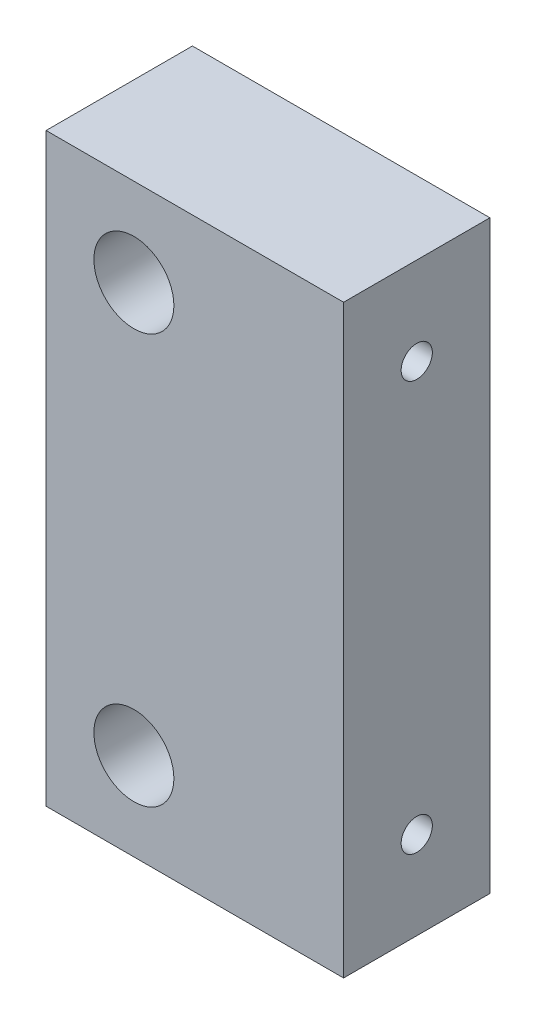
SolidWorks part; units mm, degrees
ref_plane "Front Plane" through (0, 0, 0) normal (0, 0, 1) x (1, 0, 0)
ref_plane "Top Plane" through (0, 0, 0) normal (0, 1, 0) x (1, 0, 0)
ref_plane "Right Plane" through (0, 0, 0) normal (1, 0, 0) x (0, 0, -1)
sketch "Sketch1" plane through (0, 0, 0) normal (0, 1, 0) x (1, 0, 0)
  line L1 (-15.25, 7.5) -> (15.25, 7.5)
  line L2 (-15.25, 7.5) -> (-15.25, -7.5)
  line L3 (-15.25, -7.5) -> (15.25, -7.5)
  line L4 (15.25, 7.5) -> (15.25, -7.5)
  point P4 (0, 7.5)
  point P6 (15.25, 0)
  dimension "D1" = 15
  dimension "D2" = 30.5
extrude "Boss-Extrude1" add sketch "Sketch1" along normal blind 60
sketch "Sketch2" plane through (0, 0, 7.5) normal (0, 0, 1) x (1, 0, 0)
  line L2 (-15.25, 0) -> (15.25, 0) construction
  line L4 (-15.25, 60) -> (-15.25, 0) construction
  circle A0 centre (-6.25, 51) radius 4.1
  circle A1 centre (-6.25, 9) radius 4.1
  dimension "D1" = 9
  dimension "D2" = 42
  dimension "D3" = 9
  dimension "D4" = 9
extrude "Cut-Extrude1" cut sketch "Sketch2" against normal through all
sketch "Sketch3" plane through (15.25, 0, 0) normal (1, 0, 0) x (0, 0, -1)
  line L0 (-7.5, 60) -> (7.5, 60) construction
  line L1 (-7.5, 0) -> (7.5, 0) construction
  line L2 (-7.5, 60) -> (-7.5, 0) construction
  circle A0 centre (0, 51) radius 1.6
  circle A1 centre (0, 9) radius 1.6
  dimension "D1" = 9
  dimension "D2" = 9
  dimension "D3" = 7.5
extrude "Cut-Extrude2" cut sketch "Sketch3" against normal blind 15
